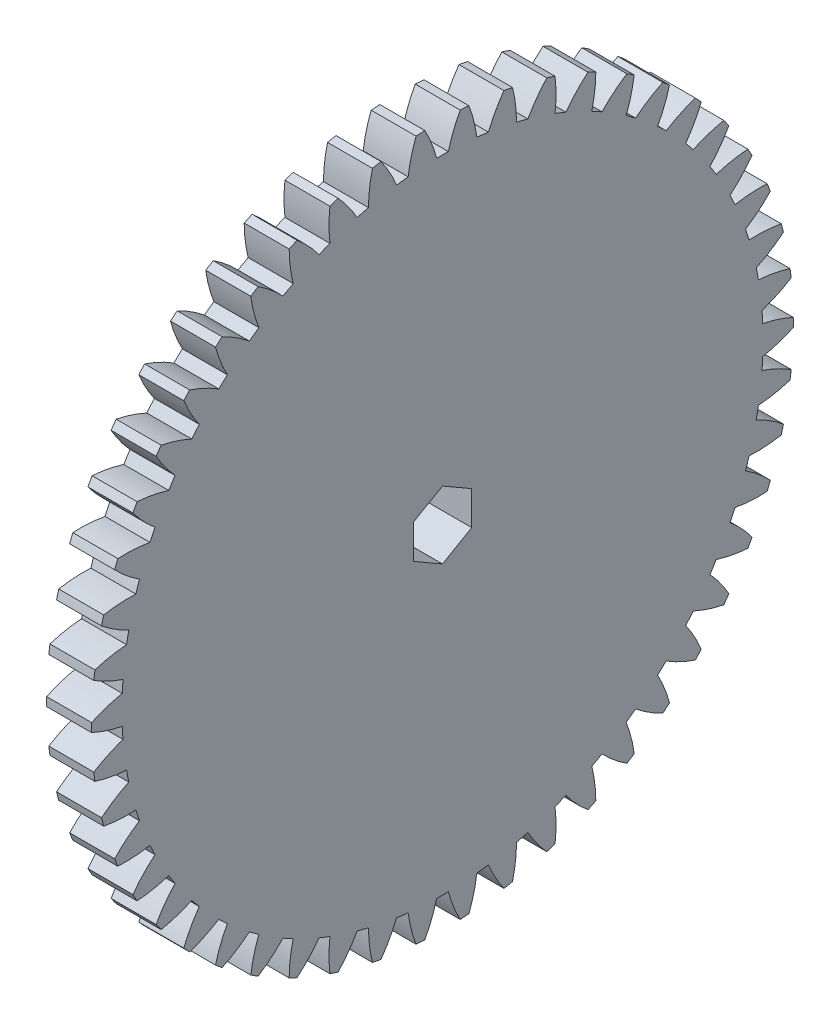
SolidWorks part; units mm, degrees
ref_plane "Plane1" through (0, 0, 0) normal (0, 0, 1) x (1, 0, 0)
ref_plane "Plane2" through (0, 0, 0) normal (0, 1, 0) x (1, 0, 0)
ref_plane "Plane3" through (0, 0, 0) normal (1, 0, 0) x (0, 0, -1)
sketch "HoldingSke" plane through (0, 0, 0) normal (0, 1, 0) x (1, 0, 0)
  line L0 (0, 0) -> (0.4285, -0.5107)
  line L1 (-15, 0) -> (100, 0) construction
  line L2 (0, 0) -> (-2.1039, 2.3779)
  line L3 (0, 0) -> (-11.863, 4.5341)
  line L4 (0, 0) -> (5.5511, 6.6156)
  line L5 (0, 0) -> (-46.8476, -17.4728)
  line L6 (0, 0) -> (-4.1448, -2.7965)
  line L7 (-2.1039, 2.3779) -> (8.6586, 51.2059)
  line L8 (-76.2, 54.61) -> (-75.3, 54.61)
  line L9 (-71.009, 38.7566) -> (-53.1078, 45.2721)
  line L10 (-76.2, 71.12) -> (104.1128, 71.12)
  line L11 (0, 0) -> (-5, 0)
  line L12 (-76.2, 101.6) -> (-76.147, 101.6)
  line L13 (24.9733, 27.94) -> (52.9518, 28.4284)
  line L14 (24.9733, 27.94) -> (24.9743, 27.94)
  line L15 (24.9733, 27.94) -> (100.4006, 29.5858)
  line L16 (-63.627, -1.5) -> (-12.827, -1.5)
  circle A0 centre (0, 0) radius 2.5
  circle A1 centre (0, 0) radius 35.624
  circle A2 centre (0, 0) radius 37.5
  circle A3 centre (0, 0) radius 2.5
  dimension "MHD" = 71.248
  dimension "Hub_dia" = 75
  dimension "Bore" = 5
  dimension "MBD" = 5
  dimension "Num_teeth" = 50
  dimension "Pitch" = 0.6667
  dimension "Overall_len" = 50
  dimension "Show_teeth" = 50
  dimension "Thickness" = 5
  dimension "OAL" = 50.0001
  dimension "T_dim" = 0.9
  dimension "Ap" = 20
  dimension "H" = 19.05
  dimension "Pitch_radius" = 180.3128
  dimension "Width" = 5
  dimension "Backlash" = 0.053
  dimension "Addendum_fac" = 1
  dimension "Dedendum_fac" = 1.25
  dimension "Clearance_fac" = 0.25
  dimension "Dedendum_add" = 0.001
  dimension "Module" = 1.5
sketch "BasProSke" plane through (0, 0, 0) normal (0, 1, 0) x (1, 0, 0)
  line L0 (-10, 0) -> (60, 0) construction
  line L1 (0, 0) -> (0, 39)
  line L2 (0, 0) -> (5, 0)
  line L3 (5, 0) -> (5, 39)
  line L4 (5, 39) -> (0, 39)
  dimension "Thickness" = 5
  dimension "Diameter" = 78
revolve "Base-Revolve" add sketch "BasProSke" angle 360 about L0
sketch "TooCutSke" plane through (0, 0, 0) normal (1, 0, 0) x (0, 0, -1)
  line L1 (0, 0) -> (0, 107) construction
  line L2 (0, 0) -> (-1.2706, 37.4785) construction
  line L3 (0, 0) -> (-4.7073, 74.8207) construction
  line L4 (-1.2706, 37.4785) -> (-2.3537, 37.4103) construction
  arc A0 (0.65, 35.6181) -> (-0.65, 35.6181) centre (0, 0) ccw
  arc A1 (1.9801, 38.9751) -> (-1.9801, 38.9751) centre (0, 0) ccw
  circle A2 centre (0, 0) radius 37.5 construction
  circle A3 centre (0, 0) radius 35.2385 construction
  arc A4 (-0.65, 35.6181) -> (-1.9801, 38.9751) centre (-15.1589, 31.8113) ccw
  arc A5 (1.9801, 38.9751) -> (0.65, 35.6181) centre (15.1589, 31.8113) ccw
  dimension "Root_dia" = 71.248
  dimension "Overcut_dia" = 78.0508
  dimension "Pitch_dia" = 75
  dimension "Base_dia" = 70.4769
  dimension "Flank_rad" = 15
  dimension "Half_ang" = 3.6
  dimension "Half_CT" = 1.0852
extrude "ToothCut" cut sketch "TooCutSke" along normal through all
fillet "Breaks" [suppressed] radius 0.03
fillet "RootFillets" [suppressed] radius 0.376
pattern_circular "TeethCuts" count 50 every 7.2 about axis through (-10, 0, 0) along (1, 0, 0) of "ToothCut", "RootFillets", "Breaks"
sketch "HubNeaOneSke" plane through (0, 0, 0) normal (-1, 0, 0) x (0, 0, 1)
  circle A0 centre (0, 0) radius 35.624
  dimension "Diameter" = 71.248
extrude "HubNearOne" [suppressed] add sketch "HubNeaOneSke" along normal blind 45.0001
sketch "HubNeaBotSke" plane through (0, 0, 0) normal (-1, 0, 0) x (0, 0, 1)
  circle A0 centre (0, 0) radius 35.624
  dimension "Diameter" = 71.248
extrude "HubNearBoth" [suppressed] add sketch "HubNeaBotSke" along normal blind 22.5
ref_plane "FarPln" through (5, 0, 0) normal (1, 0, 0) x (0, 0, -1)
sketch "HubFarSke" plane through (5, 0, 0) normal (1, 0, 0) x (0, 0, -1)
  circle A0 centre (0, 0) radius 35.624
  dimension "Diameter" = 71.248
extrude "HubFar" [suppressed] add sketch "HubFarSke" along normal blind 22.5
sketch "BorSke" plane through (0, 0, 0) normal (1, 0, 0) x (0, 0, -1)
  line L1 (0, -3.75) -> (3.2476, -1.875)
  line L2 (3.2476, -1.875) -> (3.2476, 1.875)
  line L3 (3.2476, 1.875) -> (0, 3.75)
  line L4 (0, 3.75) -> (-3.2476, 1.875)
  line L5 (-3.2476, 1.875) -> (-3.2476, -1.875)
  line L6 (-3.2476, -1.875) -> (0, -3.75)
  circle A0 centre (0, 0) radius 3.75 construction
  circle A1 centre (0, 0) radius 3.2476 construction
  dimension "Diameter" = 7.5
extrude "Bore" cut sketch "BorSke" along normal mid plane 100.0001
sketch "KeySke" plane through (0, 0, 0) normal (1, 0, 0) x (0, 0, -1)
  line L0 (-1, 0) -> (-1, 3.4)
  line L1 (-1, 3.4) -> (1, 3.4)
  line L2 (1, 3.4) -> (1, 0)
  line L3 (0, 0) -> (0, 34) construction
  line L4 (-1, 0) -> (1, 0)
  dimension "Offset" = 3.4
  dimension "Width" = 2
extrude "Keyway" [suppressed] cut sketch "KeySke" along normal mid plane 100.0001
pattern_circular "Keyway2" [suppressed] count 2 every 90 about axis through (-10, 0, 0) along (1, 0, 0)
sketch "Sketch1" plane through (0, 0, 0) normal (-1, 0, 0) x (0, 0, 1)
  line L12 (3.2476, -1.875) -> (3.2476, 1.875) construction
  line L13 (3.2476, 1.875) -> (0, 3.75) construction
  line L14 (0, 3.75) -> (-3.2476, 1.875) construction
  line L15 (-3.2476, 1.875) -> (-3.2476, -1.875) construction
  line L16 (-3.2476, -1.875) -> (0, -3.75) construction
  line L17 (0, -3.75) -> (3.2476, -1.875) construction
  line L18 (3.2476, -1.875) -> (3.2476, 1.875)
  line L19 (3.2476, 1.875) -> (0, 3.75)
  line L20 (0, 3.75) -> (-3.2476, 1.875)
  line L21 (-3.2476, 1.875) -> (-3.2476, -1.875)
  line L22 (-3.2476, -1.875) -> (0, -3.75)
  line L23 (0, -3.75) -> (3.2476, -1.875)
  line L24 (4.5499, -3.3057) -> (-4.5499, 3.3057) construction
  arc A40 (0.1868, -8.9981) -> (0.8757, -5.5554) centre (-1.8542, -6.7994) ccw
  arc A41 (-0.1868, -8.9981) -> (0.1868, -8.9981) centre (0, 0) ccw
  arc A42 (-0.8757, -5.5554) -> (-0.1868, -8.9981) centre (1.8542, -6.7994) ccw
  arc A43 (-2.5569, -5.0091) -> (-0.8757, -5.5554) centre (0, 0) ccw
  arc A44 (-5.1378, -7.3894) -> (-2.5569, -5.0091) centre (-5.4967, -4.4109) ccw
  arc A45 (-5.4401, -7.1698) -> (-5.1378, -7.3894) centre (0, 0) ccw
  arc A46 (-3.9738, -3.9797) -> (-5.4401, -7.1698) centre (-2.4965, -6.5907) ccw
  arc A47 (-5.0129, -2.5496) -> (-3.9738, -3.9797) centre (0, 0) ccw
  arc A48 (-8.4999, -2.9582) -> (-5.0129, -2.5496) centre (-7.0396, -0.3377) ccw
  arc A49 (-8.6154, -2.6029) -> (-8.4999, -2.9582) centre (0, 0) ccw
  arc A50 (-5.5541, -0.8839) -> (-8.6154, -2.6029) centre (-5.8936, -3.8646) ccw
  arc A51 (-5.5541, 0.8839) -> (-5.5541, -0.8839) centre (0, 0) ccw
  arc A52 (-8.6154, 2.6029) -> (-5.5541, 0.8839) centre (-5.8936, 3.8646) ccw
  arc A53 (-8.4999, 2.9582) -> (-8.6154, 2.6029) centre (0, 0) ccw
  arc A54 (-5.0129, 2.5496) -> (-8.4999, 2.9582) centre (-7.0396, 0.3377) ccw
  arc A55 (-3.9738, 3.9797) -> (-5.0129, 2.5496) centre (0, 0) ccw
  arc A56 (-5.4401, 7.1698) -> (-3.9738, 3.9797) centre (-2.4965, 6.5907) ccw
  arc A57 (-5.1378, 7.3894) -> (-5.4401, 7.1698) centre (0, 0) ccw
  arc A58 (-2.5569, 5.0091) -> (-5.1378, 7.3894) centre (-5.4967, 4.4109) ccw
  arc A59 (-0.8757, 5.5554) -> (-2.5569, 5.0091) centre (0, 0) ccw
  arc A60 (-0.1868, 8.9981) -> (-0.8757, 5.5554) centre (1.8542, 6.7994) ccw
  arc A61 (0.1868, 8.9981) -> (-0.1868, 8.9981) centre (0, 0) ccw
  arc A62 (0.8757, 5.5554) -> (0.1868, 8.9981) centre (-1.8542, 6.7994) ccw
  arc A63 (2.5569, 5.0091) -> (0.8757, 5.5554) centre (0, 0) ccw
  arc A64 (5.1378, 7.3894) -> (2.5569, 5.0091) centre (5.4967, 4.4109) ccw
  arc A65 (5.4401, 7.1698) -> (5.1378, 7.3894) centre (0, 0) ccw
  arc A66 (3.9738, 3.9797) -> (5.4401, 7.1698) centre (2.4965, 6.5907) ccw
  arc A67 (5.0129, 2.5496) -> (3.9738, 3.9797) centre (0, 0) ccw
  arc A68 (8.4999, 2.9582) -> (5.0129, 2.5496) centre (7.0396, 0.3377) ccw
  arc A69 (8.6154, 2.6029) -> (8.4999, 2.9582) centre (0, 0) ccw
  arc A70 (5.5541, 0.8839) -> (8.6154, 2.6029) centre (5.8936, 3.8646) ccw
  arc A71 (5.5541, -0.8839) -> (5.5541, 0.8839) centre (0, 0) ccw
  arc A72 (8.6154, -2.6029) -> (5.5541, -0.8839) centre (5.8936, -3.8646) ccw
  arc A73 (8.4999, -2.9582) -> (8.6154, -2.6029) centre (0, 0) ccw
  arc A74 (5.0129, -2.5496) -> (8.4999, -2.9582) centre (7.0396, -0.3377) ccw
  arc A75 (3.9738, -3.9797) -> (5.0129, -2.5496) centre (0, 0) ccw
  arc A76 (5.4401, -7.1698) -> (3.9738, -3.9797) centre (2.4965, -6.5907) ccw
  arc A77 (5.1378, -7.3894) -> (5.4401, -7.1698) centre (0, 0) ccw
  arc A78 (2.5569, -5.0091) -> (5.1378, -7.3894) centre (5.4967, -4.4109) ccw
  arc A79 (0.8757, -5.5554) -> (2.5569, -5.0091) centre (0, 0) ccw
extrude "Boss-Extrude1" add sketch "Sketch1" along normal blind 6
equation "' \"Module@HoldingSke\" = 6.35"
equation "' \"Num_teeth@HoldingSke\" = 12"
equation "' \"Ap@HoldingSke\" =  20"
equation "' \"Ap@HoldingSke\" = 20"
equation "' \"Width@HoldingSke\" = 0.5 * 25.4"
equation "' \"Hub_dia@HoldingSke\"= 1 * 25.4"
equation "' \"Hub_dia@HoldingSke\" = 1 * 25.4"
equation "' \"Overall_len@HoldingSke\" = 1.0 * 25.4"
equation "' \"Bore@HoldingSke\" = 0.75 * 25.4"
equation "' \"T_dim@HoldingSke\" = 0.1 * 25.4"
equation "' \"Width@KeySke\" = 0.25 * 25.4"
equation "' \"Show_teeth@HoldingSke\" = 13"
equation "' \"Backlash@HoldingSke\" = 0.009 * 25.4"
equation "' \"Addendum_fac@HoldingSke\" = 1.0"
equation "' \"Dedendum_fac@HoldingSke\" = 1.25"
equation "' \"Dedendum_add@HoldingSke\" = 0.00005 * 25.4"
equation "' \"Clearance_fac@HoldingSke\" = 0.25"
equation "\"Pitch@HoldingSke\" = 1 / \"Module@HoldingSke\""
equation "\"Overcut_dia@TooCutSke\" = (\"Num_teeth@HoldingSke\" + 2 * \"Addendum_fac@HoldingSke\") / \"Pitch@HoldingSke\" + 0.002 * 25.4"
equation "\"Pitch_dia@TooCutSke\" = \"Num_teeth@HoldingSke\" / \"Pitch@HoldingSke\""
equation "\"Base_dia@TooCutSke\" = \"Num_teeth@HoldingSke\" / \"Pitch@HoldingSke\" * cos((\"Ap@HoldingSke\"  * 3.14159265 / 180))"
equation "\"Root_dia@TooCutSke\" = (\"Num_teeth@HoldingSke\" + 2) / \"Pitch@HoldingSke\" - 2 * (\"Addendum_fac@HoldingSke\" + \"Dedendum_fac@HoldingSke\") / \"Pitch@HoldingSke\" - \"Dedendum_add@HoldingSke\" * 2"
equation "\"Half_ang@TooCutSke\" = 180 / \"Num_teeth@HoldingSke\""
equation "\"Half_CT@TooCutSke\" = \"Num_teeth@HoldingSke\" / \"Pitch@HoldingSke\" * sin((3.14159265 / 2 / \"Num_teeth@HoldingSke\")) / 2 - 7 * \"Backlash@HoldingSke\" / 4"
equation "\"Flank_rad@TooCutSke\" = \"Num_teeth@HoldingSke\" / \"Pitch@HoldingSke\" / 5"
equation "\"Radius@RootFillets\" = \"Clearance_fac@HoldingSke\" / \"Pitch@HoldingSke\" + \"Dedendum_add@HoldingSke\""
equation "\"Break_rad@Breaks\" = 0.02 / \"Pitch@HoldingSke\""
equation "\"Thickness@HoldingSke\" = \"Width@HoldingSke\""
equation "\"OAL@HoldingSke\" = \"Thickness@HoldingSke\""
equation "\"MHD@HoldingSke\" = (\"Num_teeth@HoldingSke\" + 2) / \"Pitch@HoldingSke\" - 2 * (\"Addendum_fac@HoldingSke\" + \"Dedendum_fac@HoldingSke\")  / \"Pitch@HoldingSke\" - \"Dedendum_add@HoldingSke\" * 2"
equation "\"MBD@HoldingSke\" = (\"Num_teeth@HoldingSke\" + 2) / \"Pitch@HoldingSke\" - 2 * (\"Addendum_fac@HoldingSke\" + \"Dedendum_fac@HoldingSke\")  / \"Pitch@HoldingSke\" - \"Dedendum_add@HoldingSke\" * 2 - 0.002 * 25.4"
equation "\"MHD@HoldingSke\" = ((sgn( \"MHD@HoldingSke\" - \"Hub_dia@HoldingSke\" )-1)*( \"MHD@HoldingSke\" - \"Hub_dia@HoldingSke\" ))/-2+ \"Hub_dia@HoldingSke\""
equation "\"MBD@HoldingSke\" = ((sgn( \"MBD@HoldingSke\" - \"Bore@HoldingSke\" )-1)*( \"MBD@HoldingSke\" - \"Bore@HoldingSke\" ))/-2+ \"Bore@HoldingSke\""
equation "\"OAL@HoldingSke\" = ((sgn( \"OAL@HoldingSke\" - \"Overall_len@HoldingSke\" )+1)*( \"OAL@HoldingSke\" - \"Overall_len@HoldingSke\" ))/2 + \"Overall_len@HoldingSke\" + 0.000002 * 25.4"
equation "\"Num_teeth@TeethCuts\" = int( \"Show_teeth@HoldingSke\" ) + 1"
equation "\"Num_teeth@TeethCuts\" = ((sgn( \"Num_teeth@TeethCuts\" - \"Num_teeth@HoldingSke\" )-1)*( \"Num_teeth@TeethCuts\" - \"Num_teeth@HoldingSke\" ))/-2+ \"Num_teeth@HoldingSke\""
equation "\"Num_teeth@TeethCuts\" = ((sgn( \"Num_teeth@TeethCuts\" - 2.0)+1)*( \"Num_teeth@TeethCuts\" - 2.0))/2 +2.0"
equation "\"Angle@TeethCuts\" = 360.0 / \"Num_teeth@HoldingSke\""
equation "\"Diameter@BasProSke\" = (\"Num_teeth@HoldingSke\" + 2 * \"Addendum_fac@HoldingSke\") / \"Pitch@HoldingSke\""
equation "\"Thickness@BasProSke\"  = \"Thickness@HoldingSke\""
equation "' \"Fillet_rad@BasProSke\" =  \"Thickness@HoldingSke\" * 0.05"
equation "' \"Fillet_rad@BasProSke\" = \"Thickness@HoldingSke\" * 0.05"
equation "\"MHD@HoldingSke\" = ((sgn( \"MHD@HoldingSke\" - \"Root_dia@TooCutSke\" )-1)*( \"MHD@HoldingSke\" - \"Root_dia@TooCutSke\" ))/-2+ \"Root_dia@TooCutSke\""
equation "\"Diameter@HubNeaOneSke\" = \"MHD@HoldingSke\""
equation "\"Length@HubNearOne\" = \"OAL@HoldingSke\" - \"Thickness@BasProSke\""
equation "\"Diameter@HubNeaBotSke\" = \"MHD@HoldingSke\""
equation "\"Length@HubNearBoth\" = ( \"OAL@HoldingSke\" - \"Thickness@BasProSke\" ) / 2.0"
equation "\"Thickness@FarPln\" = \"Thickness@BasProSke\""
equation "\"Diameter@HubFarSke\" = \"MHD@HoldingSke\""
equation "\"Length@HubFar\" = ( \"OAL@HoldingSke\" - \"Thickness@BasProSke\" ) / 2.0"
equation "\"D1@Bore\" = \"OAL@HoldingSke\" * 2.0"
equation "\"D1@Keyway\" = \"OAL@HoldingSke\" * 2.0"
equation "\"Offset@KeySke\" = \"T_dim@HoldingSke\" + \"MBD@HoldingSke\" / 2.0"
